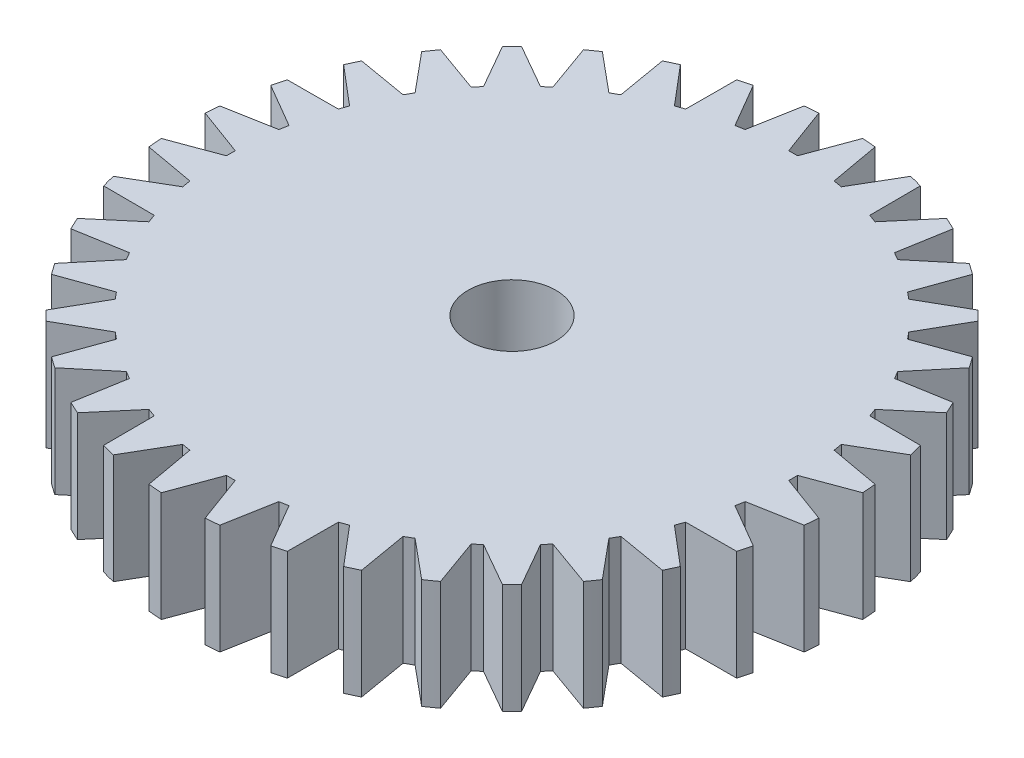
SolidWorks part; units mm, degrees
ref_plane "Front Plane" through (0, 0, 0) normal (0, 0, 1) x (1, 0, 0)
ref_plane "Top Plane" through (0, 0, 0) normal (0, 1, 0) x (1, 0, 0)
ref_plane "Right Plane" through (0, 0, 0) normal (1, 0, 0) x (0, 0, -1)
sketch "Sketch1" plane through (0, 0, 0) normal (0, 1, 0) x (1, 0, 0)
  circle A0 centre (0, 0) radius 15
  dimension "D1" = 30
extrude "Boss-Extrude1" add sketch "Sketch1" along normal blind 5
sketch "Sketch2" plane through (0, 5, 0) normal (0, 1, 0) x (1, 0, 0)
  circle A0 centre (0, 0) radius 2
  dimension "D1" = 4
extrude "Cut-Extrude1" cut sketch "Sketch2" against normal through all
sketch "Sketch3" plane through (0, 5, 0) normal (0, 1, 0) x (1, 0, 0)
  line L0 (0, 0) -> (0, 12.8) construction
  line L1 (0, 12.8) -> (0.2, 12.8)
  line L2 (0.2, 12.8) -> (1, 14.9666)
  line L3 (1, 14.9666) -> (1, 18.1147)
  line L4 (1, 18.1147) -> (-1, 18.1147)
  line L5 (-1, 18.1147) -> (-1, 14.9666)
  line L6 (-1, 14.9666) -> (-0.2, 12.8)
  line L7 (-0.2, 12.8) -> (0, 12.8)
  circle A0 centre (0, 0) radius 15 construction
  dimension "D1" = 0.2
  dimension "D2" = 0.2
  dimension "D3" = 0.8
  dimension "D4" = 0.8
  dimension "D5" = 12.8
extrude "Cut-Extrude2" cut sketch "Sketch3" against normal blind 10
pattern_circular "CirPattern1" count 36 every 10 about axis through (0, 0, 0) along (0, 1, 0) of "Cut-Extrude2"
